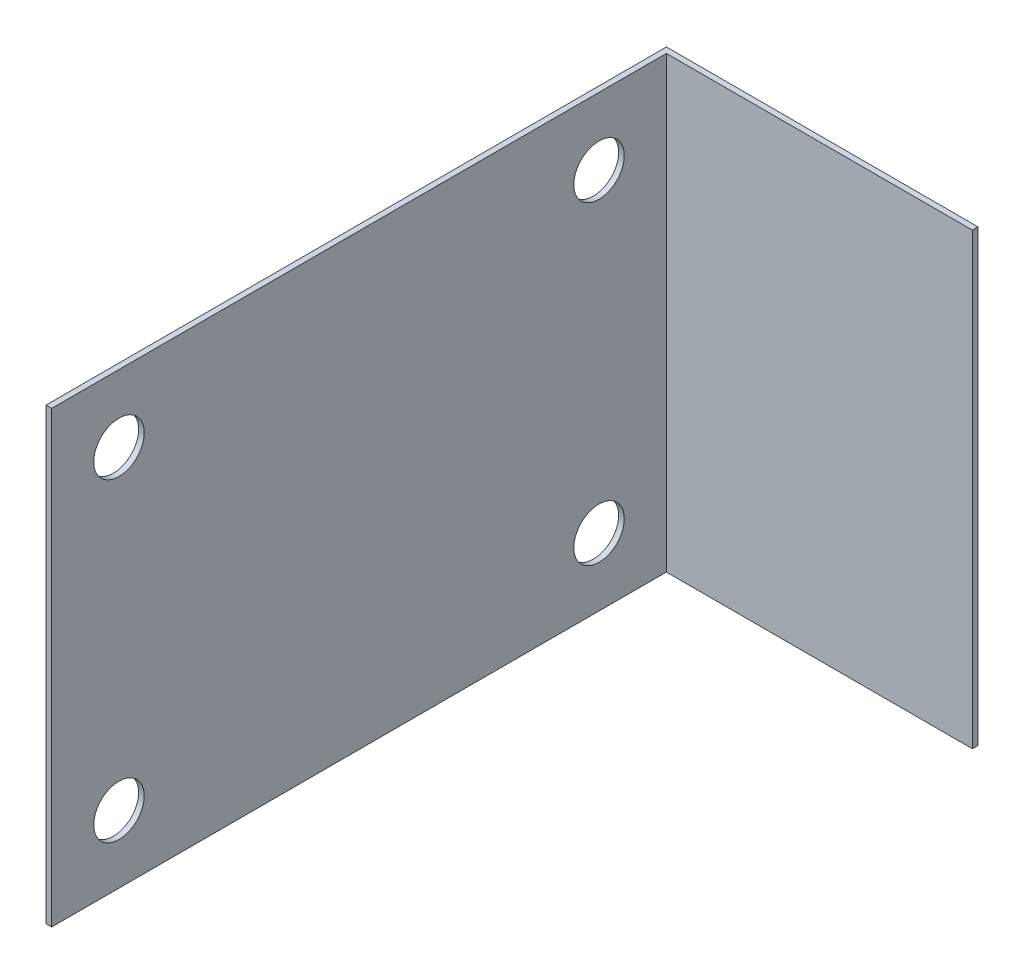
SolidWorks part; units mm, degrees
ref_plane "Front Plane" through (0, 0, 0) normal (0, 0, 1) x (1, 0, 0)
ref_plane "Top Plane" through (0, 0, 0) normal (0, 1, 0) x (1, 0, 0)
ref_plane "Right Plane" through (0, 0, 0) normal (1, 0, 0) x (0, 0, -1)
sketch "Sketch1" plane through (0, 0, 0) normal (0, 1, 0) x (1, 0, 0)
  line L0 (0, 0) -> (3.175, 0)
  line L1 (3.175, 0) -> (3.175, 347.6625)
  line L2 (3.175, 347.6625) -> (176.2125, 347.6625)
  line L3 (176.2125, 347.6625) -> (176.2125, 350.8375)
  line L4 (176.2125, 350.8375) -> (0, 350.8375)
  line L5 (0, 350.8375) -> (0, 0)
  dimension "D1" = 350.8375
  dimension "D2" = 176.2125
  dimension "D3" = 3.175
  dimension "D4" = 3.175
extrude "Boss-Extrude1" add sketch "Sketch1" along normal mid plane 254
sketch "Sketch2" plane through (3.175, 0, 0) normal (1, 0, 0) x (0, 0, -1)
  line L0 (0, 0) -> (347.6625, 0) construction
  line L1 (347.6625, 127) -> (347.6625, -127) construction
  line L2 (0, -127) -> (347.6625, -127) construction
  line L3 (173.8312, 127) -> (173.8312, -127) construction
  line L4 (0, 127) -> (347.6625, 127) construction
  circle A0 centre (309.5625, -88.9) radius 14.2748
  circle A1 centre (309.5625, 88.9) radius 14.2748
  circle A2 centre (38.1, -88.9) radius 14.2748
  circle A3 centre (38.1, 88.9) radius 14.2748
  point P19 (0, 0)
  dimension "D1" = 28.5496
  dimension "D2" = 38.1
  dimension "D3" = 38.1
extrude "Cut-Extrude1" cut sketch "Sketch2" against normal through all
equation "\"D4@Sketch1\"=\"D3@Sketch1\""
